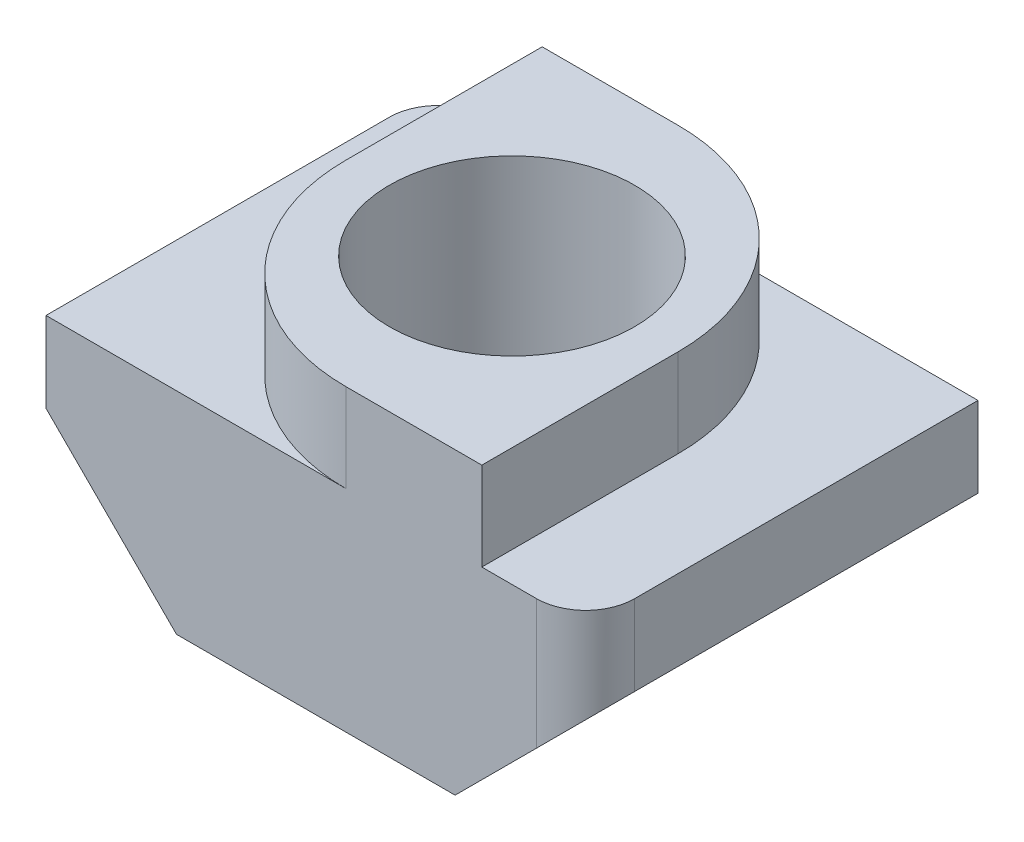
SolidWorks part; units mm, degrees
ref_plane "Front" through (0, 0, 0) normal (0, 0, 1) x (1, 0, 0)
ref_plane "Top" through (0, 0, 0) normal (0, 1, 0) x (1, 0, 0)
ref_plane "Right" through (0, 0, 0) normal (1, 0, 0) x (0, 0, -1)
sketch "Sketch1" plane through (0, 0, 0) normal (0, 1, 0) x (1, 0, 0)
  line L1 (-5.5, -4) -> (5.5, -4)
  line L2 (-5.5, -4) -> (-5.5, 4)
  line L3 (-5.5, 4) -> (5.5, 4)
  line L4 (5.5, -4) -> (5.5, 4)
  line L5 (-5.5, -4) -> (5.5, 4) construction
  line L6 (-5.5, 4) -> (5.5, -4) construction
  circle A0 centre (0, 0) radius 2.5
  point P0 (0, 0)
  dimension "D1" = 5
  dimension "D2" = 11
  dimension "D3" = 8
extrude "Boss-Extrude1" add sketch "Sketch1" along normal blind 4.3
sketch "Sketch2" plane through (0, 0, 4) normal (0, 0, 1) x (1, 0, 0)
  line L0 (-5.5, 2.66) -> (-2.84, 0)
  line L1 (-5.5, 4.3) -> (-5.5, 0) construction
  line L2 (-5.5, 0) -> (5.5, 0) construction
  line L3 (-5.5, 2.66) -> (-5.5, 0)
  line L4 (-5.5, 0) -> (-2.84, 0)
  line L5 (0, 0) -> (0, 4.3) construction
  line L6 (-5.5, 4.3) -> (5.5, 4.3) construction
  line L7 (5.5, 2.66) -> (5.5, 0)
  line L8 (5.5, 0) -> (2.84, 0)
  line L9 (5.5, 2.66) -> (2.84, 0)
  dimension "D1" = 1.64
  dimension "D2" = 45
extrude "Cut-Extrude1" cut sketch "Sketch2" against normal through all
sketch "Sketch3" plane through (0, 4.3, 0) normal (0, 1, 0) x (1, 0, 0)
  line L0 (5.5, 4) -> (-5.5, 4) construction
  line L1 (-3.385, -4) -> (3.385, -4)
  line L2 (-3.385, -4) -> (-3.385, 4)
  line L3 (-3.385, 4) -> (3.385, 4)
  line L4 (3.385, -4) -> (3.385, 4)
  line L5 (-3.385, -4) -> (3.385, 4) construction
  line L6 (-3.385, 4) -> (3.385, -4) construction
  circle A0 centre (0, 0) radius 2.5
  point P0 (0, 0)
  dimension "D2" = 5
  dimension "D1" = 6.77
extrude "Boss-Extrude2" add sketch "Sketch3" along normal blind 1.8
fillet "Fillet1" radius 4 2 edges
fillet "Fillet2" radius 1 2 edges at (5.5, 3.48, 4) (-5.5, 3.48, -4)
